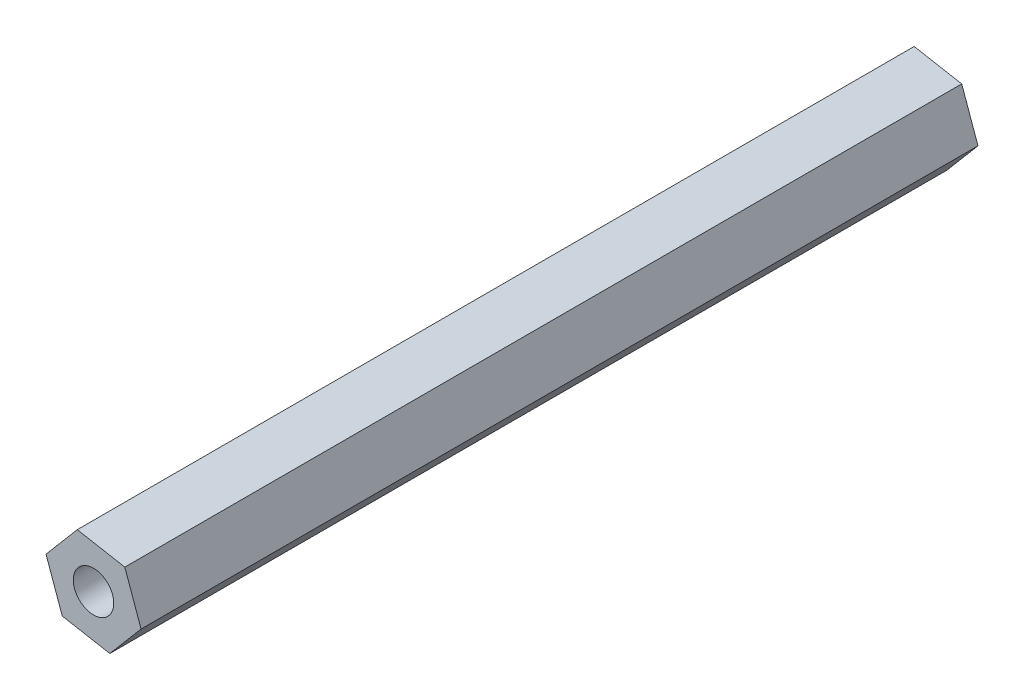
SolidWorks part; units mm, degrees
material "ABS"
ref_plane "Plano frontal" through (0, 0, 0) normal (0, 0, 1) x (1, 0, 0)
ref_plane "Plano superior" through (0, 0, 0) normal (0, 1, 0) x (1, 0, 0)
ref_plane "Plano direito" through (0, 0, 0) normal (1, 0, 0) x (0, 0, -1)
sketch "Esboço1" plane through (0, 0, 0) normal (0, 0, 1) x (1, 0, 0)
  line L1 (12.9332, -4.1439) -> (9.5251, -3.5237)
  line L2 (9.5251, -3.5237) -> (7.2839, -6.1651)
  line L3 (7.2839, -6.1651) -> (8.4508, -9.4267)
  line L4 (8.4508, -9.4267) -> (11.8589, -10.0469)
  line L5 (11.8589, -10.0469) -> (14.1001, -7.4055)
  line L6 (14.1001, -7.4055) -> (12.9332, -4.1439)
  circle A0 centre (10.692, -6.7853) radius 3 construction
extrude "Ressalto-extrusão1" add sketch "Esboço1" along normal blind 60
sketch "Esboço4" plane through (0, 0, 0) normal (0, 0, -1) x (-1, 0, 0)
  line L1 (-12.9332, -4.1439) -> (-9.5251, -3.5237) construction
  circle A0 centre (-10.692, -6.7853) radius 1.45
  dimension "D1" = 3
  dimension "D2" = 2.9
extrude "Corte-extrusão2" cut sketch "Esboço4" against normal through all
